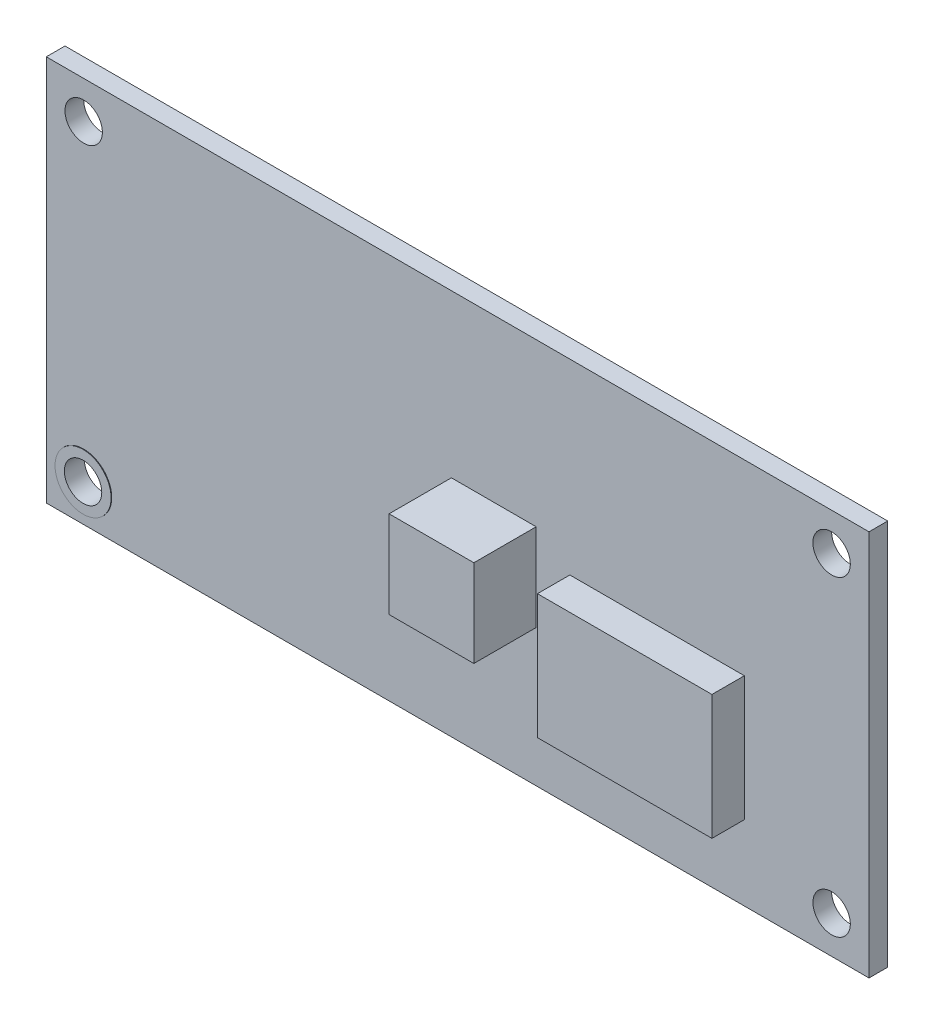
SolidWorks part; units mm, degrees
ref_plane "Front Plane" through (0, 0, 0) normal (0, 0, 1) x (1, 0, 0)
ref_plane "Top Plane" through (0, 0, 0) normal (0, 1, 0) x (1, 0, 0)
ref_plane "Right Plane" through (0, 0, 0) normal (1, 0, 0) x (0, 0, -1)
sketch "Sketch1" plane through (0, 0, 0) normal (0, 0, 1) x (1, 0, 0)
  line L0 (0, 0) -> (33, 0) construction
  line L1 (-33, 15.5) -> (33, 15.5)
  line L2 (-33, 15.5) -> (-33, -15.5)
  line L3 (-33, -15.5) -> (33, -15.5)
  line L4 (33, 15.5) -> (33, -15.5)
  line L5 (-33, 15.5) -> (33, -15.5) construction
  line L6 (-33, -15.5) -> (33, 15.5) construction
  line L7 (0, 0) -> (0, 15.5) construction
  circle A0 centre (30, 12.5) radius 1.5
  circle A1 centre (30, -12.5) radius 1.5
  circle A2 centre (-30, -12.5) radius 1.5
  circle A3 centre (-30, 12.5) radius 1.5
  point P0 (0, 0)
  dimension "D3" = 3
  dimension "D5" = 3
  dimension "D1" = 66
  dimension "D2" = 31
  dimension "D4" = 3
extrude "Boss-Extrude1" add sketch "Sketch1" along normal blind 1.5
sketch "Sketch2" plane through (0, 0, 1.5) normal (0, 0, 1) x (1, 0, 0)
  line L0 (-33, -15.5) -> (33, -15.5) construction
  line L1 (9, 0.5) -> (23, 0.5)
  line L2 (9, 0.5) -> (9, -9.5)
  line L3 (9, -9.5) -> (23, -9.5)
  line L4 (23, 0.5) -> (23, -9.5)
  line L5 (9, 0.5) -> (23, -9.5) construction
  line L6 (9, -9.5) -> (23, 0.5) construction
  line L7 (33, -15.5) -> (33, 15.5) construction
  point P0 (16, -4.5)
  dimension "D1" = 14
  dimension "D2" = 10
  dimension "D3" = 16
  dimension "D4" = 24
extrude "Boss-Extrude2" add sketch "Sketch2" along normal blind 2.6 contours L2 L1 L4 L3
sketch "Sketch3" plane through (0, 0, 1.5) normal (0, 0, 1) x (1, 0, 0)
  line L0 (33, -15.5) -> (33, 15.5) construction
  line L1 (-0.5, 2.5) -> (6.3, 2.5)
  line L2 (-0.5, 2.5) -> (-0.5, -4.5)
  line L3 (-0.5, -4.5) -> (6.3, -4.5)
  line L4 (6.3, 2.5) -> (6.3, -4.5)
  line L5 (-0.5, 2.5) -> (6.3, -4.5) construction
  line L6 (-0.5, -4.5) -> (6.3, 2.5) construction
  line L7 (33, 15.5) -> (-33, 15.5) construction
  point P0 (2.9, -1)
  dimension "D1" = 7
  dimension "D2" = 6.8
  dimension "D3" = 33.5
  dimension "D4" = 20
extrude "Boss-Extrude3" add sketch "Sketch3" along normal blind 5
sketch "Sketch4" plane through (0, 0, 1.5) normal (0, 0, 1) x (1, 0, 0)
  circle A0 centre (-30, -12.5) radius 2.25
  circle A1 centre (-30, -12.5) radius 1.5
  dimension "D1" = 4.5
extrude "Boss-Extrude4" add sketch "Sketch4" along normal blind 0.05
ref_plane "Plane1" through (0, 0, 0.75) normal (0, 0, 1) x (1, 0, 0)
mirror "Mirror1" about plane through (0, 0, 0.75) normal (0, 0, 1) of "Boss-Extrude4"
sketch "Sketch5" plane through (0, 0, 0) normal (0, 0, -1) x (-1, 0, 0)
  line L1 (19.7, -4) -> (24.9, -4)
  line L2 (19.7, -4) -> (19.7, -14)
  line L3 (19.7, -14) -> (24.9, -14)
  line L4 (24.9, -4) -> (24.9, -14)
  line L5 (19.7, -4) -> (24.9, -14) construction
  line L6 (19.7, -14) -> (24.9, -4) construction
  line L7 (33, 15.5) -> (33, -15.5) construction
  line L8 (33, -15.5) -> (-33, -15.5) construction
  line L9 (20.5, -4.8) -> (24.1, -4.8)
  line L10 (24.1, -4.8) -> (24.1, -13.2)
  line L11 (20.5, -13.2) -> (24.1, -13.2)
  line L12 (20.5, -4.8) -> (20.5, -13.2)
  point P0 (22.3, -9)
  dimension "D1" = 5.2
  dimension "D2" = 10
  dimension "D3" = 10.7
  dimension "D4" = 6.5
  dimension "D5" = 0.8
extrude "Boss-Extrude5" add sketch "Sketch5" along normal blind 10.7
chamfer "Chamfer1" distance 1 angle 45 2 edges at (-24.1, -4.8, -5.35) (-20.5, -4.8, -5.35)
fillet "Fillet1" radius 1.5 2 edges at (-19.7, -4, -5.35) (-24.9, -4, -5.35)
sketch "Sketch6" plane through (0, 0, 0) normal (0, 0, -1) x (-1, 0, 0)
  line L0 (-33, 15.5) -> (33, 15.5) construction
  line L1 (33, 15.5) -> (33, -15.5) construction
  circle A0 centre (16, 12.5) radius 1.5
  circle A1 centre (22, 12.5) radius 1.5
  point P6 (0, 0)
  dimension "D1" = 6
  dimension "D3" = 3
  dimension "D4" = 3
  dimension "D2" = 3
  dimension "D5" = 11
extrude "Boss-Extrude6" add sketch "Sketch6" along normal blind 2 contours A0 | A1
chamfer "Chamfer2" distance 1 angle 45 2 edges at (-23.5, 12.5, -2) (-17.5, 12.5, -2)
